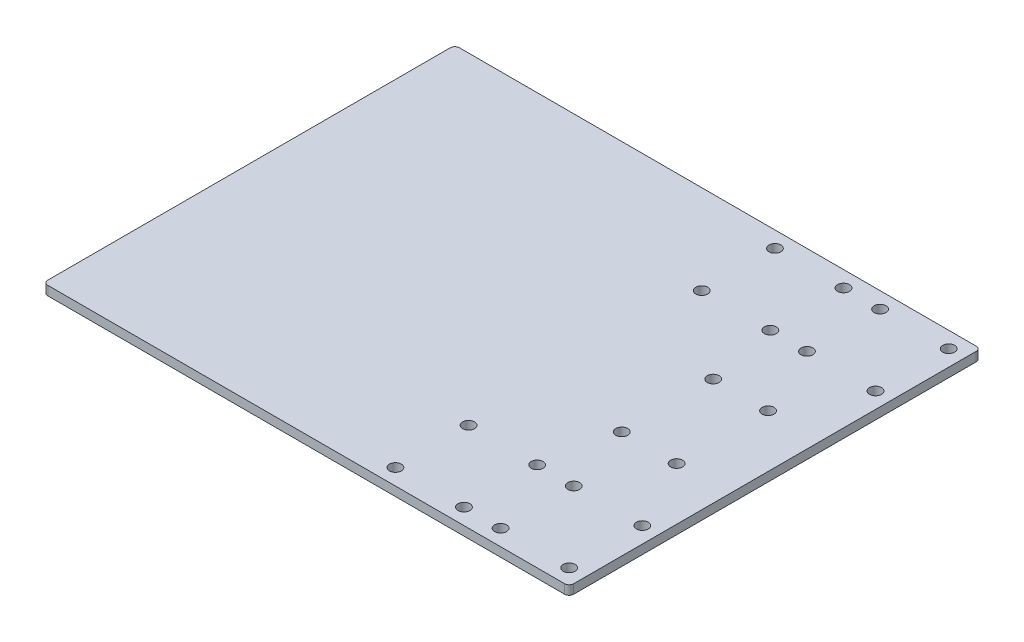
SolidWorks part; units mm, degrees
ref_plane "Спереди" through (0, 0, 0) normal (0, 0, 1) x (1, 0, 0)
ref_plane "Сверху" through (0, 0, 0) normal (0, 1, 0) x (1, 0, 0)
ref_plane "Справа" through (0, 0, 0) normal (1, 0, 0) x (0, 0, -1)
sketch "Эскиз1" plane through (0, 0, 0) normal (0, 1, 0) x (1, 0, 0)
  line L0 (230, 180) -> (230, 0)
  line L1 (0, 0) -> (230, 0)
  line L2 (0, 0) -> (0, 180)
  line L3 (0, 180) -> (230, 180)
  dimension "D1" = 180
  dimension "D2" = 230
extrude "Бобышка-Вытянуть1" add sketch "Эскиз1" along normal blind 4
hole_wizard "Диаметр отверстия Ø5.2 (5.2)1" positions "Эскиз2" profile "Эскиз3" hole size "Ø5.2" standard "Ansi Metric" end condition through all
sketch "Эскиз2" plane through (0, 4, 0) normal (0, 1, 0) x (1, 0, 0)
  line L4 (0, 0) -> (230, 0) construction
  line L5 (0, 180) -> (0, 0) construction
  line L6 (0, 90) -> (230, 90) construction
  line L11 (230, 0) -> (230, 180) construction
  point P0 (183, 70)
  point P2 (183, 110)
  point P4 (207, 70)
  point P6 (207, 110)
  point P22 (223, 39)
  point P24 (223, 7)
  point P26 (193, 7)
  point P28 (193, 39)
  point P40 (147, 39)
  point P42 (177, 39)
  point P44 (147, 7)
  point P46 (177, 7)
  point P59 (193, 173)
  point P60 (223, 173)
  point P61 (223, 141)
  point P62 (193, 141)
  point P63 (177, 173)
  point P64 (147, 173)
  point P65 (177, 141)
  point P66 (147, 141)
  dimension "D1" = 40
  dimension "D2" = 24
  dimension "D5" = 30
  dimension "D6" = 32
  dimension "D7" = 7
  dimension "D9" = 30
  dimension "D10" = 16
  dimension "D3" = 20
  dimension "D4" = 7
  dimension "D8" = 14
sketch "Эскиз3" plane through (183, 4, -70) normal (1, 0, 0) x (0, 0, 1)
  line L0 (0, 0) -> (0, 4)
  line L1 (0, 4) -> (2.6, 4)
  line L2 (2.6, 4) -> (2.6, 0)
  line L5 (2.6, 0) -> (0, 0)
  line L11 (0, -6.35) -> (0, 107.95) construction
  dimension "Диаметр сквозного отверстия" = 5.2
  dimension "Глубина сквозного отверстия" = 4
fillet "Скругление1" radius 2 4 edges at (230, 2, -180) (0, 2, -180) (0, 2, 0) (230, 2, 0)
equation "\"D9@Эскиз2\"=\"D5@Эскиз2\""
